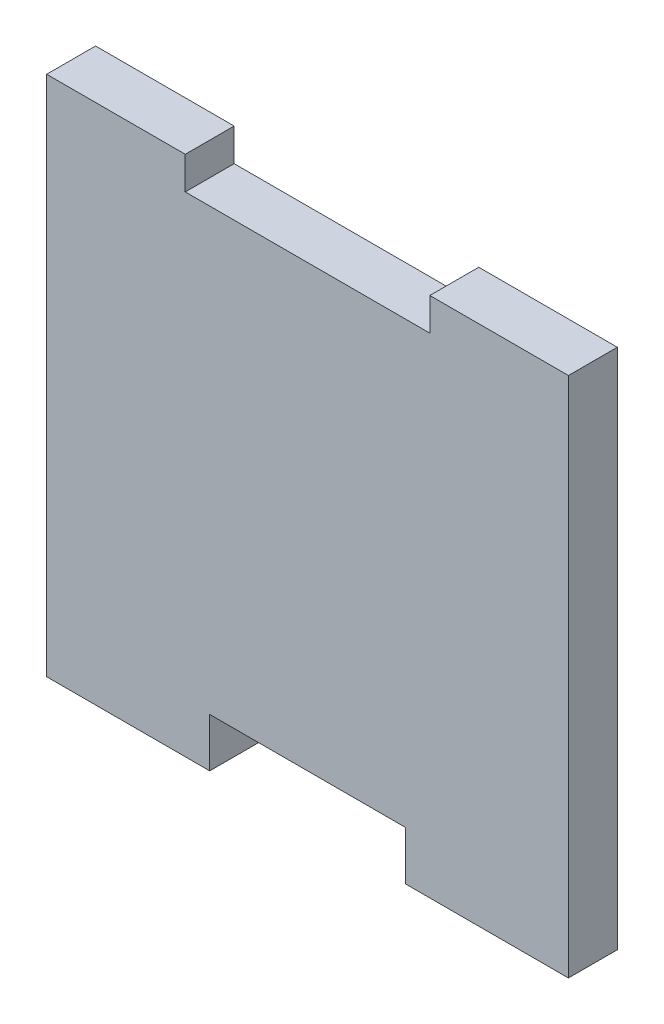
SolidWorks part; units mm, degrees
ref_plane "Alzado" through (0, 0, 0) normal (0, 0, 1) x (1, 0, 0)
ref_plane "Planta" through (0, 0, 0) normal (0, 1, 0) x (1, 0, 0)
ref_plane "Vista lateral" through (0, 0, 0) normal (1, 0, 0) x (0, 0, -1)
sketch "Model" plane through (0, 0, 0) normal (0, 0, 1) x (1, 0, 0)
  line L0 (31.8753, 32.2362) -> (23.3753, 32.2362)
  line L1 (55.3753, 0.2362) -> (55.3753, 32.2362)
  line L2 (23.3753, 32.2362) -> (23.3753, 0.2362)
  line L3 (45.3753, 3.2362) -> (45.3753, 0.2362)
  line L4 (46.8753, 30.2362) -> (46.8753, 32.2362)
  line L5 (46.8753, 30.2362) -> (31.8753, 30.2362)
  line L6 (33.3753, 3.2362) -> (33.3753, 0.2362)
  line L7 (31.8753, 32.2362) -> (31.8753, 30.2362)
  line L8 (33.3753, 3.2362) -> (45.3753, 3.2362)
  line L9 (33.3753, 0.2362) -> (23.3753, 0.2362)
  line L10 (45.3753, 0.2362) -> (55.3753, 0.2362)
  line L11 (46.8753, 32.2362) -> (55.3753, 32.2362)
extrude "Saliente-Extruir1" add sketch "Model" along normal blind 3
